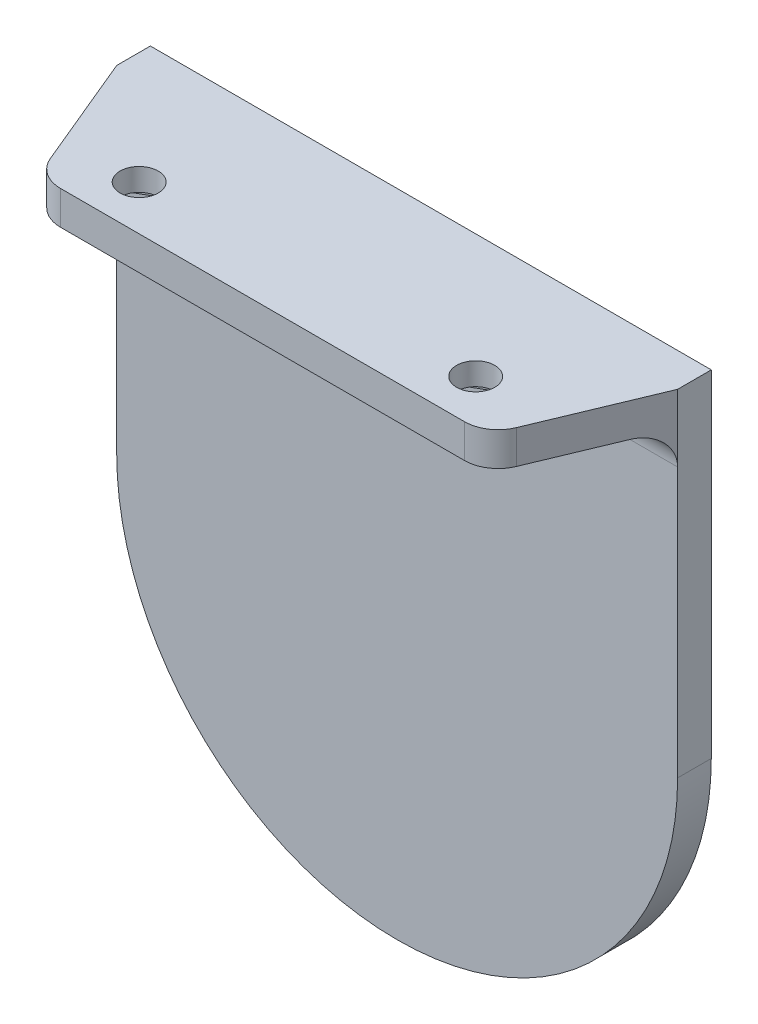
SolidWorks part; units mm, degrees
ref_plane "前视基准面" through (0, 0, 0) normal (0, 0, 1) x (1, 0, 0)
ref_plane "上视基准面" through (0, 0, 0) normal (0, 1, 0) x (1, 0, 0)
ref_plane "右视基准面" through (0, 0, 0) normal (1, 0, 0) x (0, 0, -1)
ref_plane "基准面4" through (0, 177.5, 0) normal (0, 1, 0) x (1, 0, 0)
sketch "草图1" plane through (0, 177.5, 0) normal (0, 1, 0) x (1, 0, 0)
  line L0 (920, -15) -> (925, -3)
  line L1 (925, -3) -> (875, -3)
  line L2 (875, -3) -> (880, -15)
  line L3 (880, -15) -> (920, -15)
extrude "凸台-拉伸1" add sketch "草图1" against normal blind 3
sketch "草图2" plane through (0, 0, 3) normal (0, 0, -1) x (-1, 0, 0)
  line L0 (-925, 147.5) -> (-925, 177.5)
  line L1 (-925, 177.5) -> (-875, 177.5)
  line L2 (-875, 177.5) -> (-875, 147.5)
  arc A0 (-875, 147.5) -> (-925, 147.5) centre (-900, 147.5) cw
extrude "凸台-拉伸2" add sketch "草图2" along normal blind 3
sketch "草图3" plane through (0, 174.5, 0) normal (0, -1, 0) x (1, 0, 0)
  line L0 (912.1421, 12.65) -> (912.1421, 9.35)
  line L1 (912.1421, 9.35) -> (915, 7.7)
  line L2 (915, 7.7) -> (917.8579, 9.35)
  line L3 (917.8579, 9.35) -> (917.8579, 12.65)
  line L4 (917.8579, 12.65) -> (915, 14.3)
  line L5 (915, 14.3) -> (912.1421, 12.65)
extrude "切除-拉伸1" cut sketch "草图3" against normal blind 1
sketch "草图4" plane through (0, 174.5, 0) normal (0, -1, 0) x (1, 0, 0)
  line L0 (882.1421, 9.35) -> (885, 7.7)
  line L1 (885, 7.7) -> (887.8579, 9.35)
  line L2 (887.8579, 9.35) -> (887.8579, 12.65)
  line L3 (887.8579, 12.65) -> (885, 14.3)
  line L4 (885, 14.3) -> (882.1421, 12.65)
  line L5 (882.1421, 12.65) -> (882.1421, 9.35)
extrude "切除-拉伸2" cut sketch "草图4" against normal blind 1
hole_wizard "Ø3.4 (3.4) 直径孔1" positions "草图6" profile "草图5" hole size "Ø3.4" standard "ANSI Metric"
sketch "草图6" plane through (0, 177.5, 0) normal (0, 1, 0) x (1, 0, 0)
  point P0 (885, -11)
  point P1 (915, -11)
sketch "草图5" plane through (885, 177.5, 11) normal (1, 0, 0) x (0, 0, 1)
  line L0 (0, 0) -> (0, 55)
  line L1 (0, 55) -> (1.7, 55)
  line L2 (1.7, 55) -> (1.7, 0)
  line L5 (1.7, 0) -> (0, 0)
  line L11 (0, -6.35) -> (0, 107.95) construction
  dimension "通孔孔直径" = 3.4
  dimension "通孔孔深度" = 55
fillet "圆角1" radius 3 3 edges at (920, 176, 15) (900, 174.5, 3) (880, 176, 15)
